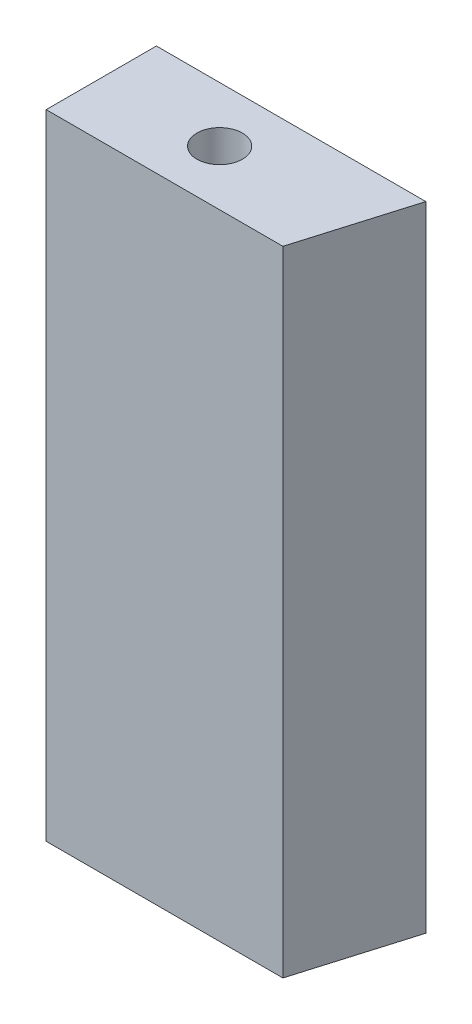
SolidWorks part; units mm, degrees
ref_plane "Front Plane" through (0, 0, 0) normal (0, 0, 1) x (1, 0, 0)
ref_plane "Top Plane" through (0, 0, 0) normal (0, 1, 0) x (1, 0, 0)
ref_plane "Right Plane" through (0, 0, 0) normal (1, 0, 0) x (0, 0, -1)
sketch "Sketch1" plane through (-73, 0, 0) normal (0, 1, 0) x (0, 0, 1)
  line L46 (82, 10.5567) -> (90, 8.1833)
  line L52 (90, -9) -> (82, -9)
  line L53 (90, -9) -> (90, 8.1833)
  line L55 (82, -9) -> (82, 10.5567)
  dimension "D1" = 19.5567
  dimension "D2" = 17.1833
  dimension "D3" = 8
extrude "Boss-Extrude1" add sketch "Sketch1" along normal blind 46
sketch "Sketch2" plane through (0, 0, 0) normal (0, -1, 0) x (1, 0, 0)
  line L0 (-82, 86) -> (-63.63, 86) construction
  line L1 (-82, 82) -> (-82, 90) construction
  line L2 (-64.8167, 90) -> (-62.4433, 82) construction
  circle A0 centre (-73.41, 86) radius 1.65
  dimension "D2" = 3.3
  dimension "D1" = 8.59
extrude "Cut-Extrude1" cut sketch "Sketch2" against normal up to next
sketch "Sketch3" plane through (-82, 0, 0) normal (-1, 0, 0) x (0, 0, 1)
  line L0 (82, 23) -> (90, 23) construction
  line L1 (82, 46) -> (82, 0) construction
  line L2 (90, 46) -> (90, 0) construction
  line L9 (86, 46) -> (86, 23) construction
  line L10 (82, 46) -> (90, 46) construction
  circle A2 centre (86, 34.5) radius 1.65
  circle A3 centre (86, 11.5) radius 1.65
  dimension "D1" = 3.3
extrude "Cut-Extrude2" cut sketch "Sketch3" against normal blind 5
